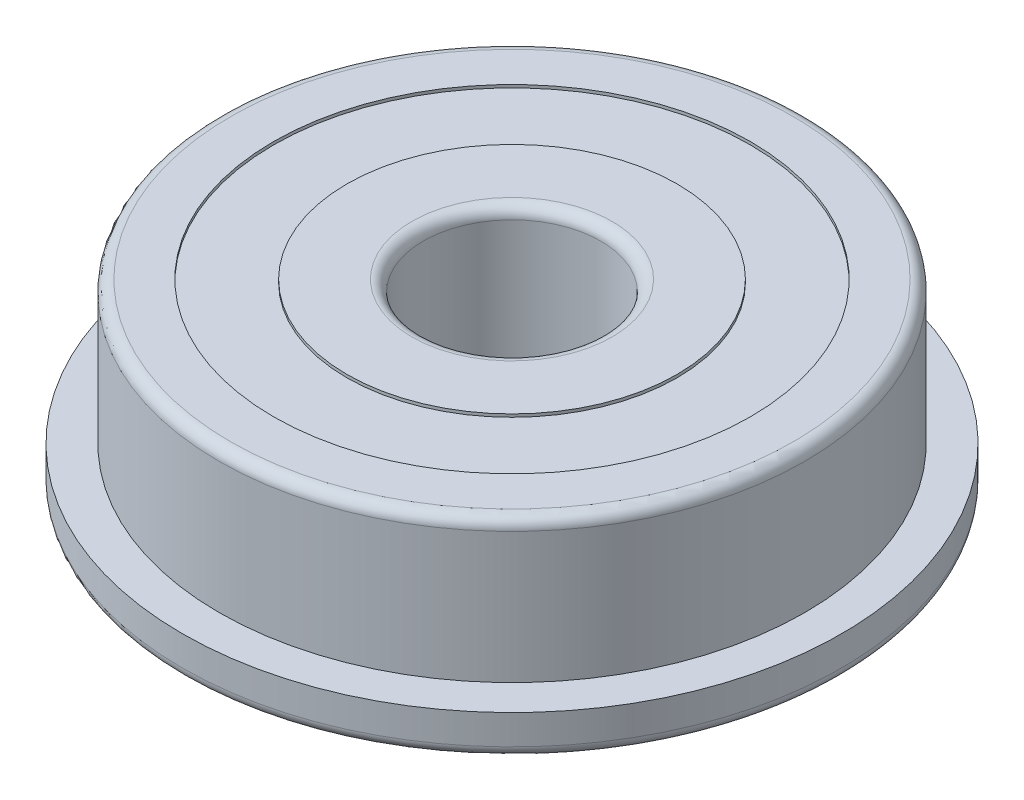
SolidWorks part; units mm, degrees
ref_plane "Front Plane" through (0, 0, 0) normal (0, 0, 1) x (1, 0, 0)
ref_plane "Top Plane" through (0, 0, 0) normal (0, 1, 0) x (1, 0, 0)
ref_plane "Right Plane" through (0, 0, 0) normal (1, 0, 0) x (0, 0, -1)
sketch "Sketch1" plane through (0, 0, 0) normal (0, 1, 0) x (1, 0, 0)
  circle A0 centre (0, 0) radius 8.985
  dimension "D1" = 17.97
extrude "Boss-Extrude1" add sketch "Sketch1" along normal blind 1.12
sketch "Sketch2" plane through (0, 1.12, 0) normal (0, 1, 0) x (1, 0, 0)
  circle A0 centre (0, 0) radius 7.985
  dimension "D1" = 15.97
extrude "Boss-Extrude2" add sketch "Sketch2" along normal blind 3.88
sketch "Sketch3" plane through (0, 5, 0) normal (0, 1, 0) x (1, 0, 0)
  circle A0 centre (0, 0) radius 2.42
  dimension "D1" = 4.84
extrude "Cut-Extrude1" cut sketch "Sketch3" against normal through all
sketch "Sketch4" plane through (0, 0, 0) normal (0, -1, 0) x (1, 0, 0)
  circle A0 centre (0, 0) radius 4.5
  circle A1 centre (0, 0) radius 6.5
  dimension "D1" = 13
  dimension "D2" = 9
extrude "Cut-Extrude2" cut sketch "Sketch4" against normal blind 0.08
sketch "Sketch5" plane through (0, 5, 0) normal (0, 1, 0) x (1, 0, 0)
  circle A0 centre (0, 0) radius 4.5
  circle A1 centre (0, 0) radius 6.5
  dimension "D1" = 13
  dimension "D2" = 9
extrude "Cut-Extrude3" cut sketch "Sketch5" against normal blind 0.08
fillet "Fillet1" radius 0.31 4 edges at (0, 0, 2.42) (0, 0, 8.985) (0, 5, 7.985) (0, 5, 2.42)
